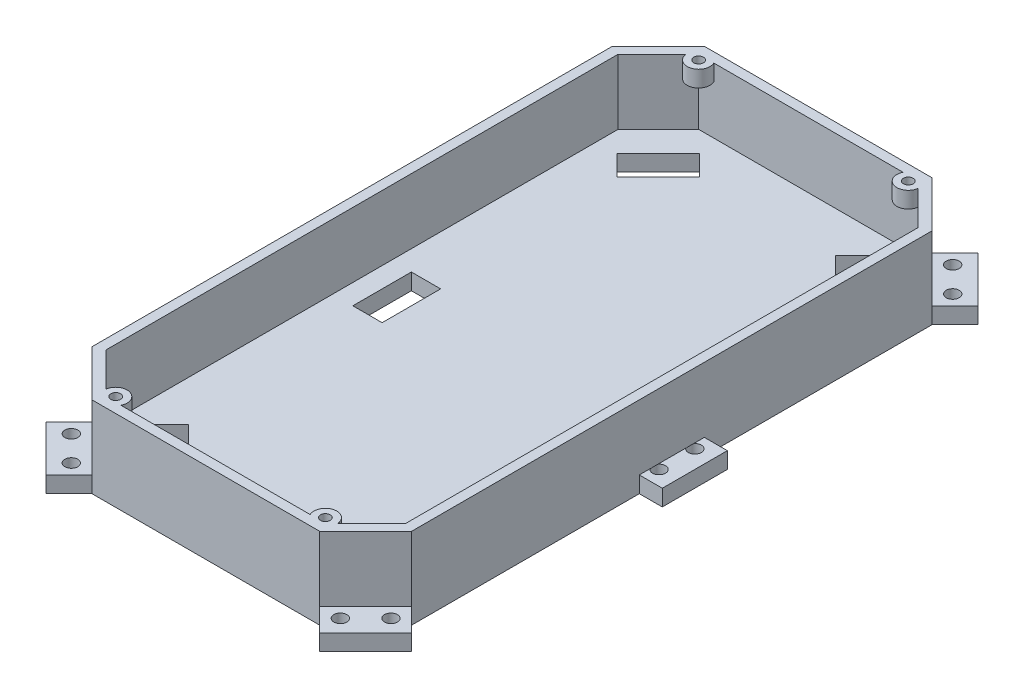
SolidWorks part; units mm, degrees
ref_plane "Front Plane" through (0, 0, 0) normal (0, 0, 1) x (1, 0, 0)
ref_plane "Top Plane" through (0, 0, 0) normal (0, 1, 0) x (1, 0, 0)
ref_plane "Right Plane" through (0, 0, 0) normal (1, 0, 0) x (0, 0, -1)
sketch "Sketch1" plane through (0, 0, 0) normal (0, 1, 0) x (1, 0, 0)
  line L1 (14.1421, 0) -> (84.1421, 0)
  line L2 (0, 14.1421) -> (0, 84.1421)
  line L3 (14.1421, 188.2843) -> (84.1421, 188.2843)
  line L4 (98.2843, 14.1421) -> (98.2843, 84.1421)
  line L5 (98.2843, 0) -> (126.5685, -28.2843)
  line L6 (-7.0711, 94.1421) -> (105.3553, 94.1421) construction
  line L7 (0, 104.1421) -> (0, 174.1421)
  line L10 (0, 104.1421) -> (-7.0711, 104.1421)
  line L11 (-7.0711, 104.1421) -> (-7.0711, 84.1421)
  line L12 (-7.0711, 181.2132) -> (0, 174.1421)
  line L13 (-7.0711, 84.1421) -> (0, 84.1421)
  line L14 (98.2843, 104.1421) -> (105.3553, 104.1421)
  line L15 (105.3553, 181.2132) -> (98.2843, 174.1421)
  line L16 (98.2843, 188.2843) -> (105.3553, 181.2132)
  line L17 (98.2843, 188.2843) -> (91.2132, 195.3553)
  line L18 (0, 188.2843) -> (-7.0711, 181.2132)
  line L19 (0, 188.2843) -> (7.0711, 195.3553)
  line L20 (7.0711, 195.3553) -> (14.1421, 188.2843)
  line L21 (91.2132, 195.3553) -> (84.1421, 188.2843)
  line L22 (105.3553, 104.1421) -> (105.3553, 84.1421)
  line L23 (105.3553, 84.1421) -> (98.2843, 84.1421)
  line L24 (98.2843, 104.1421) -> (98.2843, 174.1421)
  line L25 (0, 84.1421) -> (-7.0711, 84.1421)
  line L26 (98.2843, 84.1421) -> (105.3553, 84.1421)
  line L27 (98.2843, 84.1421) -> (98.2843, 14.1421)
  line L28 (105.3553, 7.0711) -> (98.2843, 14.1421)
  line L29 (98.2843, 0) -> (105.3553, 7.0711)
  line L30 (98.2843, 0) -> (91.2132, -7.0711)
  line L31 (91.2132, -7.0711) -> (84.1421, 0)
  line L32 (14.1421, 0) -> (84.1421, 0)
  line L33 (7.0711, -7.0711) -> (14.1421, 0)
  line L34 (0, 0) -> (7.0711, -7.0711)
  line L35 (0, 0) -> (-7.0711, 7.0711)
  line L36 (-7.0711, 7.0711) -> (0, 14.1421)
  line L37 (0, 84.1421) -> (0, 14.1421)
  dimension "D2" = 70
  dimension "D3" = 45
  dimension "D4" = 40
  dimension "D5" = 135
  dimension "D6" = 10
  dimension "D7" = 10
  dimension "D8" = 10
  dimension "D9" = 20
  dimension "D10" = 10
  dimension "D11" = 135
  dimension "D12" = 70
  dimension "D13" = 90
  dimension "D14" = 7.0711
  dimension "D15" = 10
  dimension "D16" = 10
  dimension "D17" = 20
  dimension "D18" = 7.0711
  dimension "D19" = 90
  dimension "D20" = 135
  dimension "D21" = 10
  dimension "D22" = 10
  dimension "D23" = 135
  dimension "D24" = 70
  dimension "D25" = 135
  dimension "D26" = 10
  dimension "D27" = 10
  dimension "D28" = 135
  dimension "D29" = 70
  dimension "D30" = 7.0711
  dimension "D31" = 20
  dimension "D32" = 7.0711
  dimension "D33" = 70
  dimension "D34" = 135
  dimension "D35" = 10
  dimension "D36" = 20
  dimension "D37" = 135
  dimension "D38" = 10
extrude "Boss-Extrude1" add sketch "Sketch1" along normal blind 5 contours L11 L6 L22 L14 L24 L15 L16 L17 L21 L3 L20 L19 L18 L12 L7 L10 | L6 L11 L13 L2 L36 L35 L34 L33 L1 L31 L30 L29 L28 L4 L23 L22
sketch "Sketch3" plane through (0, 0, 0) normal (0, 0, 1) x (1, 0, 0)
  line L0 (44.6452, 5) -> (44.6452, 25)
  line L1 (14.1421, 5) -> (84.1421, 5) construction
  dimension "D1" = 20
sketch "Sketch4" plane through (0, 5, 0) normal (0, 1, 0) x (1, 0, 0)
  line L0 (0, 174.1421) -> (14.1421, 188.2843)
  line L1 (14.1421, 188.2843) -> (84.1421, 188.2843)
  line L2 (84.1421, 188.2843) -> (98.2843, 174.1421)
  line L3 (98.2843, 174.1421) -> (98.2843, 14.1421)
  line L4 (98.2843, 14.1421) -> (84.1421, 0)
  line L5 (84.1421, 0) -> (14.1421, 0)
  line L6 (14.1421, 0) -> (0, 14.1421)
  line L7 (0, 14.1421) -> (0, 174.1421)
  line L8 (3, 15.3848) -> (3, 172.8995)
  line L9 (3, 172.8995) -> (15.3848, 185.2843)
  line L10 (15.3848, 185.2843) -> (82.8995, 185.2843)
  line L11 (82.8995, 185.2843) -> (95.2843, 172.8995)
  line L12 (95.2843, 172.8995) -> (95.2843, 15.3848)
  line L13 (95.2843, 15.3848) -> (82.8995, 3)
  line L14 (82.8995, 3) -> (15.3848, 3)
  line L15 (15.3848, 3) -> (3, 15.3848)
  dimension "D1" = 3
extrude "Boss-Extrude3" add sketch "Sketch4" along normal blind 20
sketch "Sketch5" plane through (0, 5, 0) normal (0, 1, 0) x (1, 0, 0)
  line L0 (98.2843, 0) -> (67.1716, 31.1127) construction
  line L1 (105.3553, 7.0711) -> (91.2132, -7.0711) construction
  line L2 (82.7279, 15.5563) -> (89.0919, 21.9203)
  line L3 (89.0919, 21.9203) -> (82.7279, 28.2843)
  line L4 (82.7279, 28.2843) -> (70, 15.5563)
  line L5 (70, 15.5563) -> (76.364, 9.1924)
  line L6 (76.364, 9.1924) -> (82.7279, 15.5563)
  line L7 (82.8995, 3) -> (95.2843, 15.3848) construction
  line L8 (105.3553, 94.1421) -> (65.0429, 94.1421) construction
  line L9 (105.3553, 104.1421) -> (105.3553, 84.1421) construction
  line L10 (89.0814, 85.1421) -> (89.0814, 103.1421)
  line L11 (89.0814, 103.1421) -> (80.0814, 103.1421)
  line L12 (80.0814, 103.1421) -> (80.0814, 85.1421)
  line L13 (80.0814, 85.1421) -> (89.0814, 85.1421)
  line L14 (89.0814, 85.1421) -> (89.0814, 92.9344)
  line L15 (89.0814, 95.3498) -> (89.0814, 92.9344)
  line L16 (49.1421, 188.2843) -> (49.1421, 0) construction
  line L17 (84.1421, 188.2843) -> (14.1421, 188.2843) construction
  line L18 (14.1421, 0) -> (84.1421, 0) construction
  line L19 (28.2843, 15.5563) -> (21.9203, 9.1924)
  line L20 (15.5563, 28.2843) -> (28.2843, 15.5563)
  line L21 (9.1924, 21.9203) -> (15.5563, 28.2843)
  line L22 (15.5563, 15.5563) -> (9.1924, 21.9203)
  line L23 (21.9203, 9.1924) -> (15.5563, 15.5563)
  line L24 (9.2028, 85.1421) -> (9.2028, 103.1421)
  line L25 (9.2028, 103.1421) -> (18.2028, 103.1421)
  line L26 (18.2028, 103.1421) -> (18.2028, 85.1421)
  line L27 (18.2028, 85.1421) -> (9.2028, 85.1421)
  line L28 (9.2028, 85.1421) -> (9.2028, 92.9344)
  line L29 (9.2028, 95.3498) -> (9.2028, 92.9344)
  line L30 (89.0814, 85.1421) -> (80.0814, 85.1421)
  line L31 (80.0814, 103.1421) -> (89.0814, 103.1421)
  line L32 (89.0814, 103.1421) -> (89.0814, 95.3498)
  line L33 (70, 172.7279) -> (76.364, 179.0919)
  line L34 (82.7279, 160) -> (70, 172.7279)
  line L35 (89.0919, 166.364) -> (82.7279, 160)
  line L36 (82.7279, 172.7279) -> (89.0919, 166.364)
  line L37 (76.364, 179.0919) -> (82.7279, 172.7279)
  line L38 (15.5563, 160) -> (28.2843, 172.7279)
  line L39 (9.1924, 166.364) -> (15.5563, 160)
  line L40 (15.5563, 172.7279) -> (9.1924, 166.364)
  line L41 (21.9203, 179.0919) -> (15.5563, 172.7279)
  line L42 (28.2843, 172.7279) -> (21.9203, 179.0919)
  line L43 (9.2028, 103.1421) -> (9.2028, 95.3498)
  line L44 (18.2028, 103.1421) -> (9.2028, 103.1421)
  line L45 (9.2028, 85.1421) -> (18.2028, 85.1421)
  point P39 (89.0814, 94.1421)
  point P50 (9.2028, 94.1421)
  dimension "D1" = 18
  dimension "D2" = 9
  dimension "D3" = 9
  dimension "D4" = 9
  dimension "D5" = 9
  dimension "D6" = 18
extrude "Cut-Extrude3" cut sketch "Sketch5" against normal blind 20 contours L5 L6 L2 L3 L4 | L23 L19 L20 L21 L22 | L27 L26 L25 L24 | L12 L13 L10 L11 | L37 L33 L34 L35 L36 | L38 L42 L41 L40 L39
sketch "Sketch6" plane through (0, 25, 0) normal (0, 1, 0) x (1, 0, 0)
  line L0 (15.3848, 185.2843) -> (20.4813, 180.1877) construction
  line L1 (49.1421, 188.2843) -> (49.1421, 174.5482) construction
  line L2 (84.1421, 188.2843) -> (14.1421, 188.2843) construction
  line L3 (3, 94.1421) -> (28.1068, 94.1421) construction
  line L4 (3, 172.8995) -> (3, 15.3848) construction
  circle A0 centre (16.9077, 183.7613) radius 1.5
  circle A1 centre (16.9077, 183.7613) radius 3.5
  circle A2 centre (81.3766, 183.7613) radius 1.5
  circle A3 centre (81.3766, 183.7613) radius 3.5
  circle A4 centre (81.3766, 4.5229) radius 3.5
  circle A5 centre (81.3766, 4.5229) radius 1.5
  circle A6 centre (16.9077, 4.5229) radius 3.5
  circle A7 centre (16.9077, 4.5229) radius 1.5
  dimension "D1" = 3
  dimension "D2" = 2
extrude "Boss-Extrude4" add sketch "Sketch6" against normal blind 5
sketch "Sketch7" plane through (0, 5, 0) normal (0, 1, 0) x (1, 0, 0)
  circle A0 centre (7.7782, 188.2843) radius 2
  circle A1 centre (0, 180.5061) radius 2
  circle A2 centre (90.5061, 188.2843) radius 2
  circle A3 centre (98.2843, 180.5061) radius 2
  circle A4 centre (99.8553, 99.6421) radius 2
  circle A5 centre (99.8553, 88.6421) radius 2
  circle A6 centre (98.2843, 7.7782) radius 2
  circle A7 centre (90.5061, 0) radius 2
  circle A8 centre (7.7782, 0) radius 2
  circle A9 centre (0, 7.7782) radius 2
  circle A10 centre (-1.5711, 88.6421) radius 2
  circle A11 centre (-1.5711, 99.6421) radius 2
extrude "Cut-Extrude4" cut sketch "Sketch7" against normal blind 5
